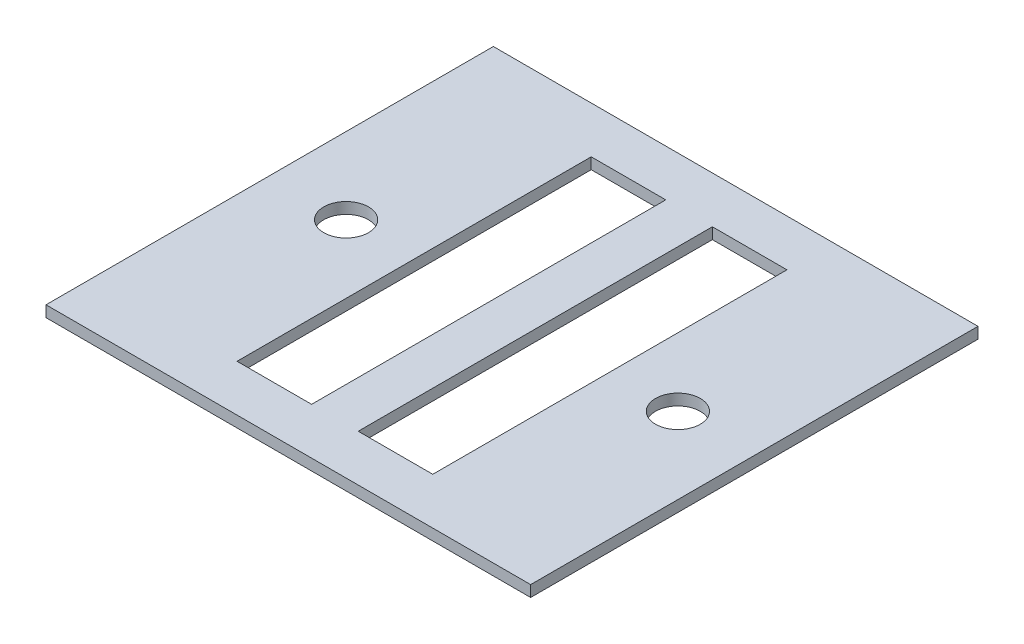
SolidWorks part; units mm, degrees
ref_plane "Front Plane" through (0, 0, 0) normal (0, 0, 1) x (1, 0, 0)
ref_plane "Top Plane" through (0, 0, 0) normal (0, 1, 0) x (1, 0, 0)
ref_plane "Right Plane" through (0, 0, 0) normal (1, 0, 0) x (0, 0, -1)
sketch "Sketch1" plane through (0, 0, 0) normal (0, 1, 0) x (1, 0, 0)
  line L1 (-65, -60) -> (65, -60)
  line L2 (-65, -60) -> (-65, 60)
  line L3 (-65, 60) -> (65, 60)
  line L4 (65, -60) -> (65, 60)
  line L5 (-65, -60) -> (65, 60) construction
  line L6 (-65, 60) -> (65, -60) construction
  point P0 (0, 0)
  dimension "D1" = 130
  dimension "D2" = 120
extrude "Boss-Extrude1" add sketch "Sketch1" along normal blind 3
sketch "Sketch2" plane through (0, 3, 0) normal (0, 1, 0) x (1, 0, 0)
  line L1 (-26.25, -47.5) -> (-6.25, -47.5)
  line L2 (-26.25, -47.5) -> (-26.25, 47.5)
  line L3 (-26.25, 47.5) -> (-6.25, 47.5)
  line L4 (-6.25, -47.5) -> (-6.25, 47.5)
  line L5 (-26.25, -47.5) -> (-6.25, 47.5) construction
  line L6 (-26.25, 47.5) -> (-6.25, -47.5) construction
  point P0 (-16.25, 0)
  dimension "D1" = 95
  dimension "D2" = 20
  dimension "D3" = 6.25
extrude "Cut-Extrude1" cut sketch "Sketch2" against normal through all both and the other way through all
mirror "Mirror1" about plane through (0, 0, 0) normal (1, 0, 0) of "Cut-Extrude1"
sketch "Sketch3" plane through (0, 3, 0) normal (0, 1, 0) x (1, 0, 0)
  circle A0 centre (44.5, 0) radius 6
  dimension "D1" = 12
  dimension "D2" = 44.5
extrude "Cut-Extrude2" cut sketch "Sketch3" against normal through all both and the other way through all
mirror "Mirror2" about plane through (0, 0, 0) normal (1, 0, 0) of "Cut-Extrude2"
